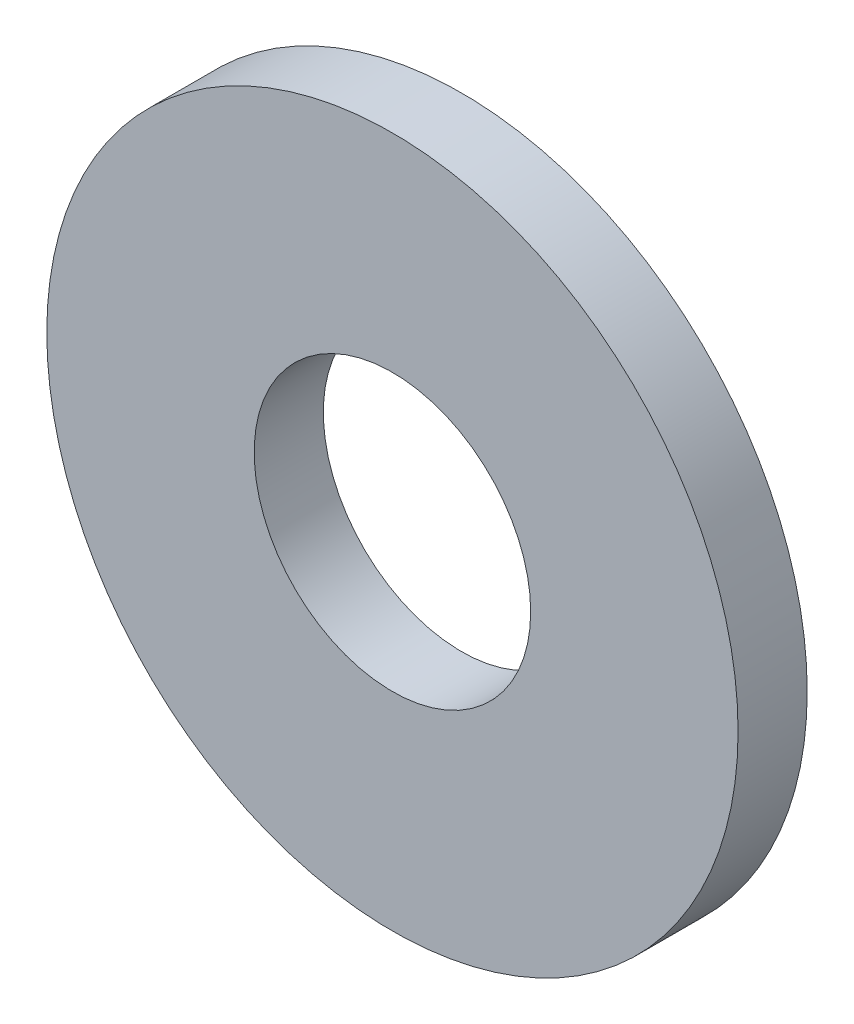
SolidWorks part; units mm, degrees
ref_plane "前视基准面" through (0, 0, 0) normal (0, 0, 1) x (1, 0, 0)
ref_plane "上视基准面" through (0, 0, 0) normal (0, 1, 0) x (1, 0, 0)
ref_plane "右视基准面" through (0, 0, 0) normal (1, 0, 0) x (0, 0, -1)
sketch "草图1" plane through (0, 0, 0) normal (0, 0, 1) x (1, 0, 0)
  circle A0 centre (0, 0) radius 1
  circle A1 centre (0, 0) radius 2.5
  dimension "D1" = 5
  dimension "D2" = 2
extrude "凸台-拉伸1" add sketch "草图1" along normal mid plane 0.5
